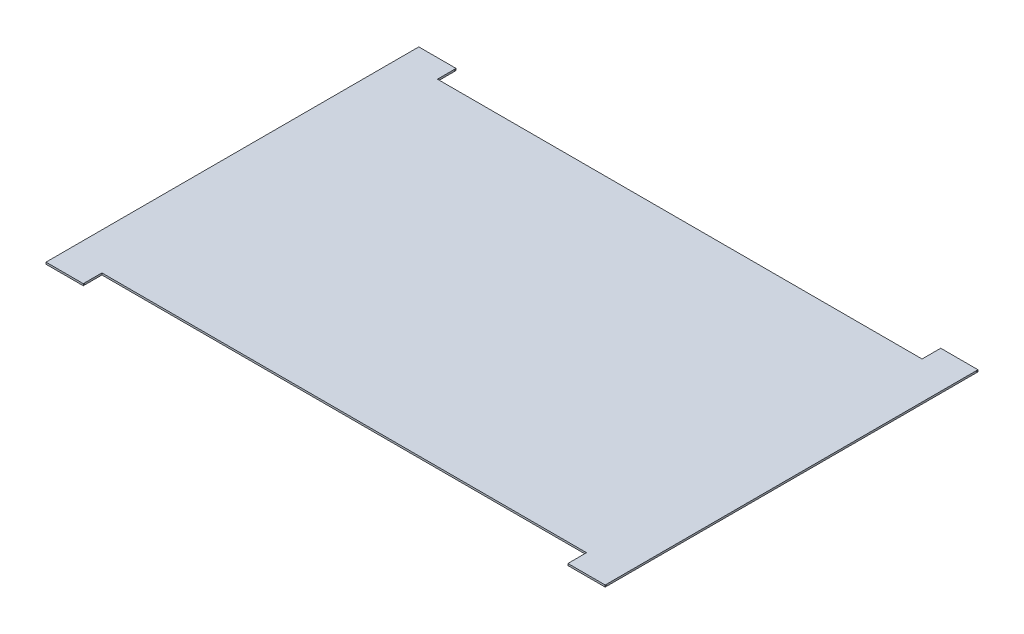
SolidWorks part; units mm, degrees
ref_plane "Alzado" through (0, 0, 0) normal (0, 0, 1) x (1, 0, 0)
ref_plane "Planta" through (0, 0, 0) normal (0, 1, 0) x (1, 0, 0)
ref_plane "Vista lateral" through (0, 0, 0) normal (1, 0, 0) x (0, 0, -1)
sketch "Croquis1" plane through (0, 0, 0) normal (0, 1, 0) x (1, 0, 0)
  line L0 (0, 10) -> (2.6993, 10) construction
  line L1 (0, 0) -> (30, 0)
  line L2 (0, 0) -> (0, 20)
  line L3 (0, 20) -> (30, 20)
  line L4 (30, 0) -> (30, 20)
  line L5 (2, 20) -> (28, 20)
  line L6 (2, 20) -> (2, 19)
  line L7 (2, 19) -> (28, 19)
  line L8 (28, 20) -> (28, 19)
  line L9 (28, 0) -> (28, 1)
  line L10 (2, 0) -> (2, 1)
  line L11 (2, 1) -> (28, 1)
  dimension "D1" = 20
  dimension "D2" = 30
  dimension "D3" = 1
  dimension "D4" = 2
  dimension "D5" = 2
extrude "Saliente-Extruir1" add sketch "Croquis1" along normal blind 0.1
sketch "Croquis2" plane through (30, 0, 0) normal (1, 0, 0) x (0, 0, -1)
  line L0 (20, 0.05) -> (19.95, 0.05) construction
  line L1 (20, 0.1) -> (20, 0) construction
  line L2 (10, 0.1) -> (10, 1.1889) construction
  line L3 (0, 0.1) -> (20, 0.1) construction
  circle A0 centre (19.95, 0.05) radius 0.025
  circle A1 centre (0.05, 0.05) radius 0.025
  dimension "D1" = 0.05
  dimension "D2" = 0.05
extrude "Cortar-Extruir1" cut sketch "Croquis2" against normal up to surface (30 mm away) up to face at (0, 0.05, -10)
